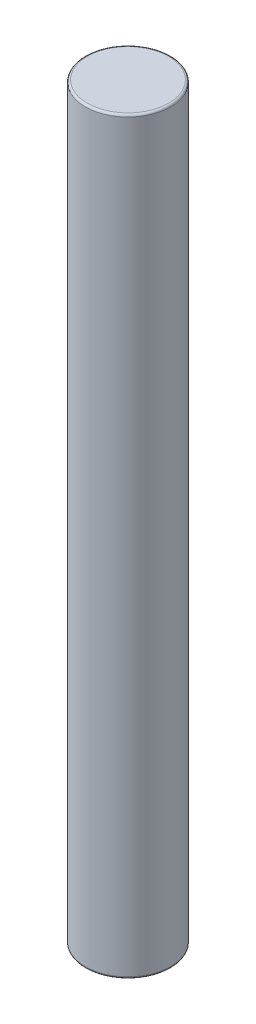
SolidWorks part; units mm, degrees
ref_plane "Front Plane" through (0, 0, 0) normal (0, 0, 1) x (1, 0, 0)
ref_plane "Top Plane" through (0, 0, 0) normal (0, 1, 0) x (1, 0, 0)
ref_plane "Right Plane" through (0, 0, 0) normal (1, 0, 0) x (0, 0, -1)
sketch "Sketch1" plane through (0, 0, 0) normal (0, 1, 0) x (1, 0, 0)
  circle A0 centre (0, 0) radius 4
extrude "Boss-Extrude1" add sketch "Sketch1" along normal blind 70
fillet "Fillet1" radius 0.2 2 edges at (0, 0, 4) (0, 70, 4)
